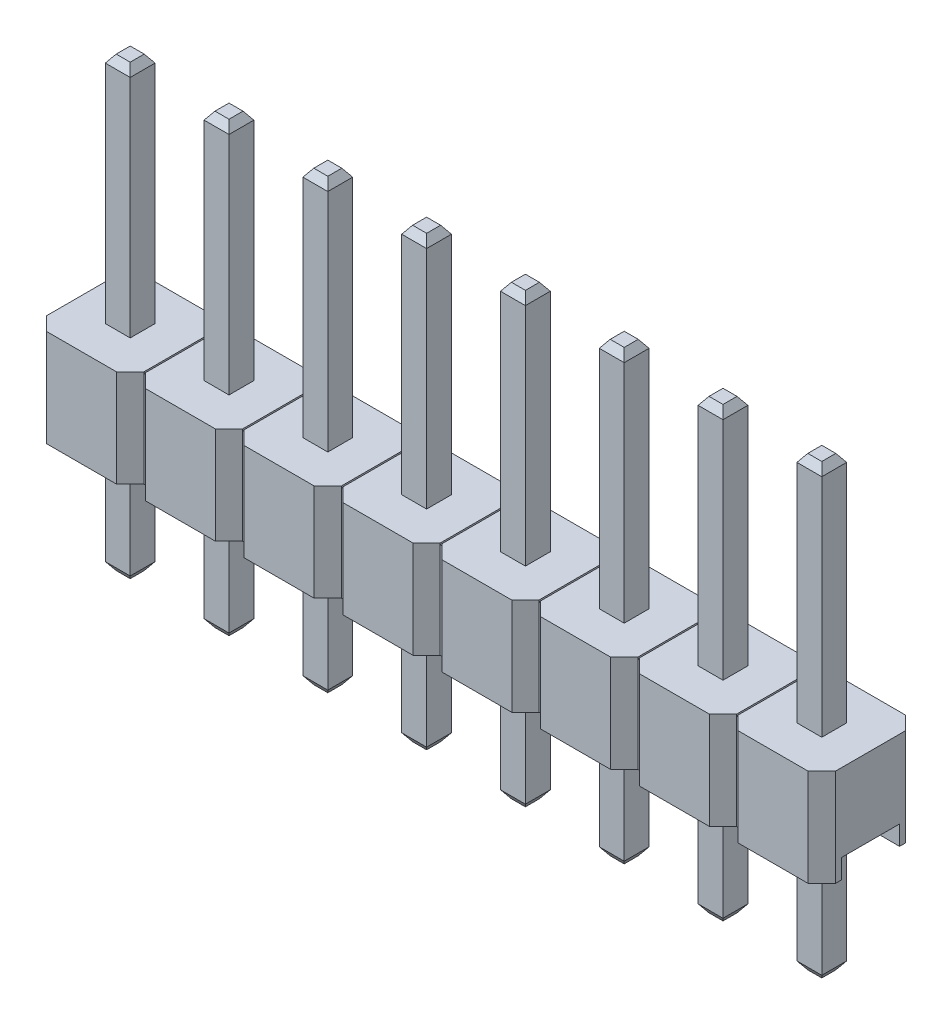
SolidWorks part; units mm, degrees
ref_plane "Front Plane" through (0, 0, 0) normal (0, 0, 1) x (1, 0, 0)
ref_plane "Top Plane" through (0, 0, 0) normal (0, 1, 0) x (1, 0, 0)
ref_plane "Right Plane" through (0, 0, 0) normal (1, 0, 0) x (0, 0, -1)
sketch "Sketch1" plane through (0, 0, 0) normal (0, 1, 0) x (1, 0, 0)
  line L0 (0, 2.15) -> (0.35, 2.5)
  line L1 (0.35, 0) -> (2.15, 0)
  line L2 (0, 0.35) -> (0, 2.15)
  line L3 (0.35, 2.5) -> (2.15, 2.5)
  line L5 (2.15, 2.5) -> (2.5, 2.15)
  line L6 (0, 0.35) -> (0.35, 0)
  line L7 (2.15, 0) -> (2.5, 0.35)
  line L9 (2.54, 0.35) -> (2.89, 0)
  line L10 (2.54, 2.15) -> (2.89, 2.5)
  line L11 (2.89, 0) -> (4.69, 0)
  line L12 (4.69, 0) -> (5.04, 0.35)
  line L14 (4.69, 2.5) -> (5.04, 2.15)
  line L15 (2.89, 2.5) -> (4.69, 2.5)
  line L17 (5.08, 0.35) -> (5.43, 0)
  line L18 (5.08, 2.15) -> (5.43, 2.5)
  line L19 (5.43, 0) -> (7.23, 0)
  line L20 (7.23, 0) -> (7.58, 0.35)
  line L22 (7.23, 2.5) -> (7.58, 2.15)
  line L23 (5.43, 2.5) -> (7.23, 2.5)
  line L25 (7.62, 0.35) -> (7.97, 0)
  line L26 (7.62, 2.15) -> (7.97, 2.5)
  line L27 (7.97, 0) -> (9.77, 0)
  line L28 (9.77, 0) -> (10.12, 0.35)
  line L30 (9.77, 2.5) -> (10.12, 2.15)
  line L31 (7.97, 2.5) -> (9.77, 2.5)
  line L33 (10.16, 0.35) -> (10.51, 0)
  line L34 (10.16, 2.15) -> (10.51, 2.5)
  line L35 (10.51, 0) -> (12.31, 0)
  line L36 (12.31, 0) -> (12.66, 0.35)
  line L38 (12.31, 2.5) -> (12.66, 2.15)
  line L39 (10.51, 2.5) -> (12.31, 2.5)
  line L41 (12.7, 0.35) -> (13.05, 0)
  line L42 (12.7, 2.15) -> (13.05, 2.5)
  line L43 (13.05, 0) -> (14.85, 0)
  line L44 (14.85, 0) -> (15.2, 0.35)
  line L46 (14.85, 2.5) -> (15.2, 2.15)
  line L47 (13.05, 2.5) -> (14.85, 2.5)
  line L49 (15.24, 0.35) -> (15.59, 0)
  line L50 (15.24, 2.15) -> (15.59, 2.5)
  line L51 (15.59, 0) -> (17.39, 0)
  line L52 (17.39, 0) -> (17.74, 0.35)
  line L54 (17.39, 2.5) -> (17.74, 2.15)
  line L55 (15.59, 2.5) -> (17.39, 2.5)
  line L57 (17.78, 0.35) -> (18.13, 0)
  line L58 (17.78, 2.15) -> (18.13, 2.5)
  line L59 (18.13, 0) -> (19.93, 0)
  line L60 (19.93, 0) -> (20.28, 0.35)
  line L61 (20.28, 0.35) -> (20.28, 2.15)
  line L62 (19.93, 2.5) -> (20.28, 2.15)
  line L63 (18.13, 2.5) -> (19.93, 2.5)
  line L64 (0, 0.35) -> (2.54, 0.35) construction
  line L65 (2.5, 2.15) -> (2.54, 2.15)
  line L66 (17.78, 0.35) -> (17.74, 0.35)
  line L67 (5.04, 2.15) -> (5.08, 2.15)
  line L68 (2.54, 0.35) -> (2.54, 2.15) [skipped]
  line L69 (5.08, 0.35) -> (5.08, 2.15) [skipped]
  line L70 (7.58, 2.15) -> (7.62, 2.15)
  line L71 (7.62, 0.35) -> (7.62, 2.15) [skipped]
  line L72 (10.12, 2.15) -> (10.16, 2.15)
  line L73 (10.16, 0.35) -> (10.16, 2.15) [skipped]
  line L74 (12.66, 2.15) -> (12.7, 2.15)
  line L75 (12.7, 0.35) -> (12.7, 2.15) [skipped]
  line L76 (15.24, 0.35) -> (15.24, 2.15) [skipped]
  line L77 (17.78, 0.35) -> (17.78, 2.15) [skipped]
  line L78 (17.74, 2.15) -> (17.78, 2.15)
  line L79 (15.2, 2.15) -> (15.24, 2.15)
  line L80 (12.7, 0.35) -> (12.66, 0.35)
  line L81 (10.16, 0.35) -> (10.12, 0.35)
  line L82 (7.62, 0.35) -> (7.58, 0.35)
  line L83 (5.08, 0.35) -> (5.04, 0.35)
  line L84 (2.54, 0.35) -> (2.5, 0.35)
  line L85 (15.24, 0.35) -> (15.2, 0.35)
  point P0 (0, 0)
  point P1 (2.5, 2.5)
  point P2 (0, 2.5)
  point P3 (2.5, 0)
  point P15 (0, 0)
  dimension "D2" = 2.5
  dimension "D3" = 2.5
  dimension "D4" = 2.54
extrude "Boss-Extrude1" add sketch "Sketch1" along normal blind 2.5
sketch "Sketch2" plane through (0, 0, 0) normal (0, -1, 0) x (1, 0, 0)
  line L0 (0, -1.25) -> (20.28, -1.25) construction
  line L1 (0, -2.15) -> (0, -0.35) construction
  line L2 (20.28, -0.35) -> (20.28, -2.15) construction
  line L4 (20.28, -2) -> (0, -2)
  line L5 (20.28, -2) -> (20.28, -0.5)
  line L6 (20.28, -0.5) -> (0, -0.5)
  line L7 (0, -2) -> (0, -0.5)
  line L8 (20.28, -2) -> (0, -0.5) construction
  line L9 (20.28, -0.5) -> (0, -2) construction
  point P6 (10.14, -1.25)
  dimension "D1" = 1.5
extrude "Cut-Extrude1" cut sketch "Sketch2" against normal blind 0.5
sketch "Sketch4" plane through (0, 2.5, 0) normal (0, 1, 0) x (1, 0, 0)
  line L0 (5.08, 2.15) -> (5.08, 0.35)
  line L1 (2.5, 2.15) -> (2.54, 2.15)
  line L2 (2.5, 2.15) -> (2.5, 0.35)
  line L3 (2.5, 0.35) -> (2.54, 0.35)
  line L4 (2.54, 2.15) -> (2.54, 0.35)
  line L5 (5.04, 2.15) -> (5.04, 0.35)
  line L6 (5.04, 2.15) -> (5.08, 2.15)
  line L7 (5.04, 0.35) -> (5.08, 0.35)
  line L8 (7.62, 2.15) -> (7.62, 0.35)
  line L9 (7.58, 2.15) -> (7.58, 0.35)
  line L10 (7.58, 2.15) -> (7.62, 2.15)
  line L11 (7.58, 0.35) -> (7.62, 0.35)
  line L12 (10.16, 2.15) -> (10.16, 0.35)
  line L13 (10.12, 2.15) -> (10.12, 0.35)
  line L14 (10.12, 2.15) -> (10.16, 2.15)
  line L15 (10.12, 0.35) -> (10.16, 0.35)
  line L16 (12.7, 2.15) -> (12.7, 0.35)
  line L17 (12.66, 2.15) -> (12.66, 0.35)
  line L18 (12.66, 2.15) -> (12.7, 2.15)
  line L19 (12.66, 0.35) -> (12.7, 0.35)
  line L20 (15.24, 2.15) -> (15.24, 0.35)
  line L21 (15.2, 2.15) -> (15.2, 0.35)
  line L22 (15.2, 2.15) -> (15.24, 2.15)
  line L23 (15.2, 0.35) -> (15.24, 0.35)
  line L24 (17.78, 2.15) -> (17.78, 0.35)
  line L25 (17.74, 2.15) -> (17.74, 0.35)
  line L26 (17.74, 2.15) -> (17.78, 2.15)
  line L27 (17.74, 0.35) -> (17.78, 0.35)
  line L28 (2.54, 2.15) -> (5.08, 2.15) construction
  dimension "D1" = 2.54
extrude "Cut-Extrude2" cut sketch "Sketch4" against normal blind 0.04
sketch "Sketch3" plane through (0, 2.5, 0) normal (0, 1, 0) x (1, 0, 0)
  line L0 (1.25, 2.5) -> (1.25, 0) construction
  line L1 (2.15, 2.5) -> (0.35, 2.5) construction
  line L2 (0.35, 0) -> (2.15, 0) construction
  line L3 (0, 1.25) -> (1.25, 1.25) construction
  line L4 (0, 2.15) -> (0, 0.35) construction
  line L6 (0.93, 0.93) -> (1.57, 0.93)
  line L7 (0.93, 0.93) -> (0.93, 1.57)
  line L8 (0.93, 1.57) -> (1.57, 1.57)
  line L9 (1.57, 0.93) -> (1.57, 1.57)
  line L10 (0.93, 0.93) -> (1.57, 1.57) construction
  line L11 (0.93, 1.57) -> (1.57, 0.93) construction
  dimension "D1" = 0.64
extrude "Boss-Extrude2" add sketch "Sketch3" along normal blind 6 and the other way blind 5.5
chamfer "Chamfer1" distance 0.2 angle 35 8 edges at (1.25, -3, -1.57) (0.93, -3, -1.25) (1.25, -3, -0.93) (1.57, -3, -1.25) (1.25, 8.5, -0.93) (0.93, 8.5, -1.25) (1.25, 8.5, -1.57) (1.57, 8.5, -1.25)
pattern_linear "LPattern1" count 8 spacing 2.54 along (1, 0, 0) of "Chamfer1", "Boss-Extrude2"
